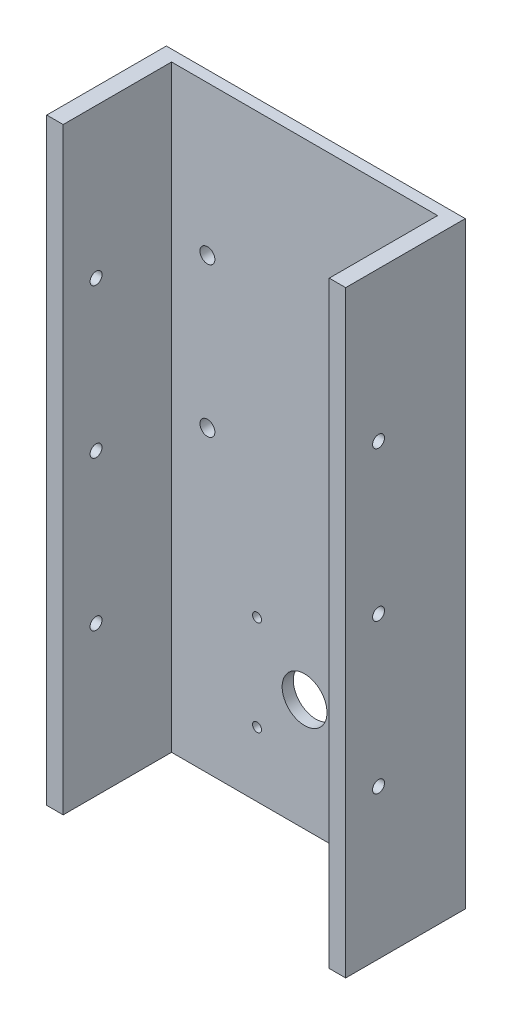
SolidWorks part; units mm, degrees
ref_plane "Front Plane" through (0, 0, 0) normal (0, 0, 1) x (1, 0, 0)
ref_plane "Top Plane" through (0, 0, 0) normal (0, 1, 0) x (1, 0, 0)
ref_plane "Right Plane" through (0, 0, 0) normal (1, 0, 0) x (0, 0, -1)
sketch "Sketch1" plane through (0, 0, 0) normal (0, 0, 1) x (1, 0, 0)
  line L17 (100, 200) -> (100, -200)
  line L18 (100, -200) -> (-100, -200)
  line L19 (-100, -200) -> (-100, 200)
  line L20 (-100, 200) -> (100, 200)
  circle A4 centre (0, -125) radius 15
  circle A13 centre (-65, 0) radius 5
  circle A14 centre (-65, 100) radius 5
  circle A15 centre (65, 100) radius 5
  circle A16 centre (65, 0) radius 5
  point P0 (0, 0)
  dimension "D7" = 30
  dimension "D1" = 100
  dimension "D2" = 130
  dimension "D3" = 10
extrude "Boss-Extrude1" add sketch "Sketch1" along normal blind 7.5
sketch "Sketch4" plane through (0, 0, 7.5) normal (0, 0, 1) x (1, 0, 0)
  line L0 (-100, 200) -> (-89, 200)
  line L1 (100, 200) -> (-100, 200) construction
  line L2 (-89, 200) -> (-89, -200)
  line L3 (-100, -200) -> (100, -200) construction
  line L4 (-89, -200) -> (-100, -200)
  line L5 (-100, -200) -> (-100, 200)
  line L6 (100, 200) -> (89, 200)
  line L7 (89, 200) -> (89, -200)
  line L8 (89, -200) -> (100, -200)
  line L9 (100, -200) -> (100, 200)
extrude "Boss-Extrude4" add sketch "Sketch4" along normal blind 72.5
sketch "Sketch5" plane through (100, 0, 0) normal (1, 0, 0) x (0, 0, -1)
  line L0 (-80, -200) -> (0, -200) construction
  line L2 (-80, -200) -> (-80, 200) construction
  circle A0 centre (-58, 100) radius 4
  circle A1 centre (-58, 0) radius 4
  circle A2 centre (-58, -100) radius 4
  dimension "D1" = 100
  dimension "D3" = 8
  dimension "D2" = 22
extrude "Cut-Extrude1" cut sketch "Sketch5" against normal blind 200
sketch "Sketch6" plane through (0, 0, 0) normal (0, 0, 1) x (1, 0, 0)
  line L0 (0, -70.1176) -> (0, -173.9118) construction
  line L1 (39.7985, -93.2002) -> (39.7985, -156.8012)
  line L2 (58.8746, -125) -> (-59.1411, -125)
  line L3 (31.7973, -93.2027) -> (0, -125)
  line L5 (31.7998, -164.8) -> (-31.8012, -164.8)
  line L6 (-39.8, -156.8012) -> (-39.8, -93.2002)
  line L7 (-31.8012, -85.2015) -> (31.7998, -85.2015)
  circle A0 centre (0, -125) radius 15 construction
  circle A1 centre (0, -125) radius 15
  circle A2 centre (0, -125) radius 45
  circle A3 centre (31.7973, -93.2027) radius 3
  circle A4 centre (-31.7973, -93.2027) radius 3
  circle A5 centre (-31.7973, -156.7973) radius 3
  circle A6 centre (31.7973, -156.7973) radius 3
  ellipse E1 centre (31.7973, -93.2027) end of major axis (37.4559, -87.5441) minor radius 8 (39.7985, -93.2002) -> (31.7998, -85.2015) ccw
  ellipse E3 centre (-31.7988, -93.2027) end of major axis (-26.1402, -98.8613) minor radius 8 (-31.8012, -85.2015) -> (-39.8, -93.2002) ccw
  ellipse E6 centre (31.7973, -156.7988) end of major axis (37.4559, -162.4574) minor radius 8 (31.7998, -164.8) -> (39.7985, -156.8012) ccw
  ellipse E7 centre (-31.7988, -156.7988) end of major axis (-37.4574, -162.4574) minor radius 8 (-39.8, -156.8012) -> (-31.8012, -164.8) ccw
  dimension "D1" = 90
  dimension "D2" = 6
extrude "Cut-Extrude2" cut sketch "Sketch6" along normal blind 10
